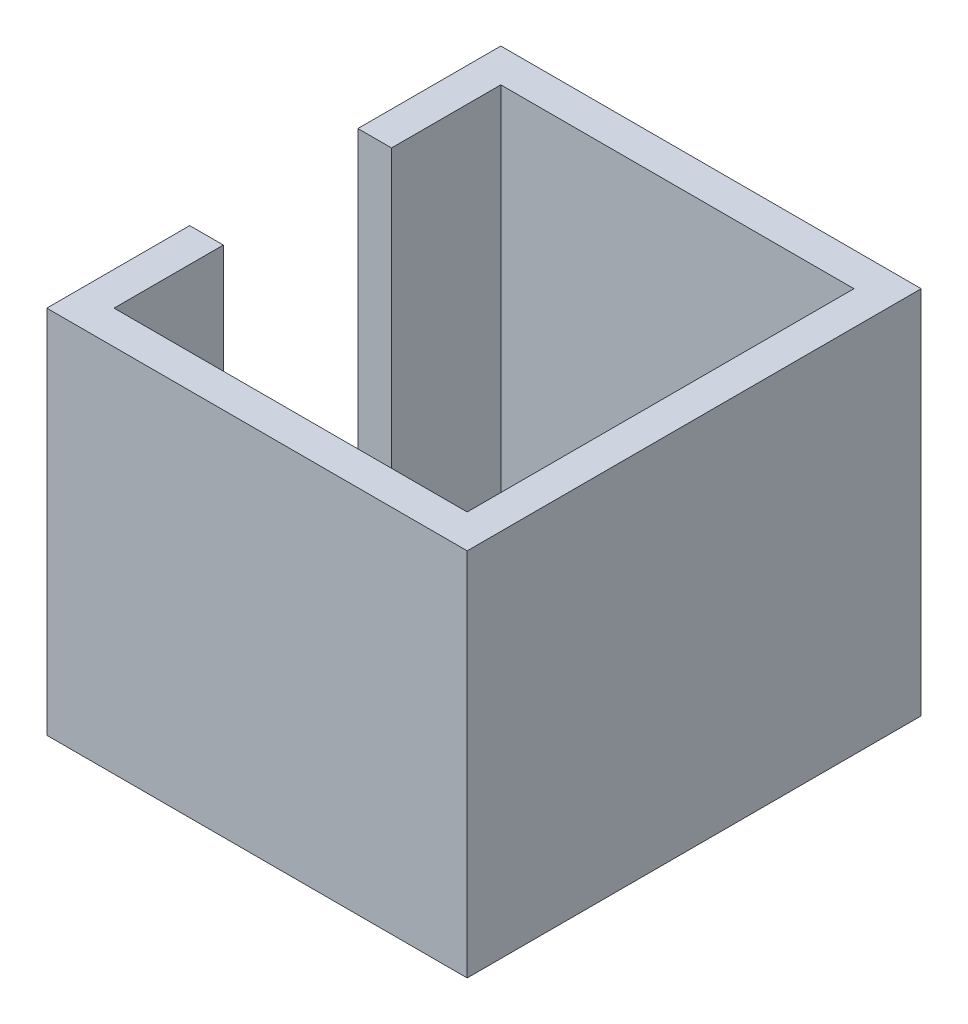
SolidWorks part; units mm, degrees
ref_plane "Front Plane" through (0, 0, 0) normal (0, 0, 1) x (1, 0, 0)
ref_plane "Top Plane" through (0, 0, 0) normal (0, 1, 0) x (1, 0, 0)
ref_plane "Right Plane" through (0, 0, 0) normal (1, 0, 0) x (0, 0, -1)
sketch "Sketch1" plane through (0, 0, 0) normal (0, 1, 0) x (1, 0, 0)
  line L0 (-10.5, 11.5) -> (10.5, 11.5)
  line L1 (-12.5, 13.5) -> (12.5, 13.5)
  line L2 (-12.5, 13.5) -> (-12.5, -13.5)
  line L3 (-12.5, -13.5) -> (12.5, -13.5)
  line L4 (12.5, 13.5) -> (12.5, -13.5)
  line L5 (-12.5, 13.5) -> (12.5, -13.5) construction
  line L6 (-12.5, -13.5) -> (12.5, 13.5) construction
  line L7 (10.5, 11.5) -> (10.5, -11.5)
  line L8 (-10.5, -11.5) -> (10.5, -11.5)
  line L9 (-10.5, 11.5) -> (-10.5, -11.5)
  point P0 (0, 0)
  dimension "D1" = 25
  dimension "D2" = 27
  dimension "D3" = 2
extrude "Boss-Extrude1" add sketch "Sketch1" along normal mid plane 22
sketch "Sketch2" plane through (0, 0, 0) normal (1, 0, 0) x (0, 0, -1)
  line L0 (13.5, 11) -> (-13.5, 11) construction
  line L1 (5, -6) -> (-5, -6)
  line L2 (5, -6) -> (5, 11)
  line L3 (5, 11) -> (-5, 11)
  line L4 (-5, -6) -> (-5, 11)
  line L5 (5, -6) -> (-5, 11) construction
  line L6 (5, 11) -> (-5, -6) construction
  line L7 (13.5, -11) -> (-13.5, -11) construction
  point P0 (0, 2.5)
  point P9 (0, 0)
  dimension "D1" = 5
  dimension "D2" = 10
extrude "Cut-Extrude1" cut sketch "Sketch2" against normal blind 3 from surface at -10.5 starting at face at (-10.5, 0, 0)
